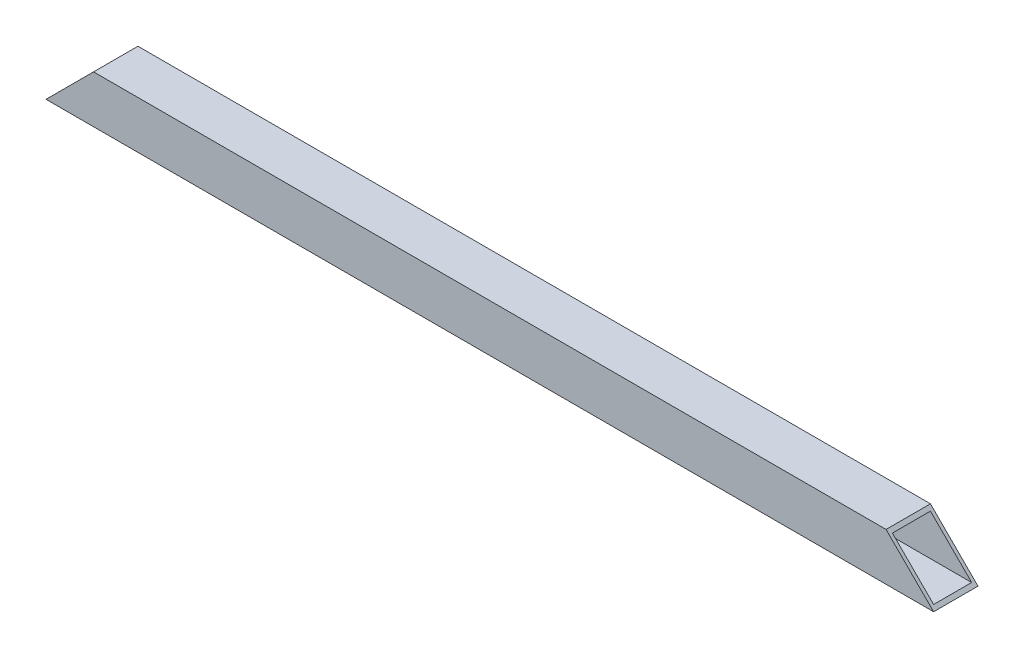
SolidWorks part; units mm, degrees
ref_plane "Спереди" through (0, 0, 0) normal (0, 0, 1) x (1, 0, 0)
ref_plane "Сверху" through (0, 0, 0) normal (0, 1, 0) x (1, 0, 0)
ref_plane "Справа" through (0, 0, 0) normal (1, 0, 0) x (0, 0, -1)
sketch "Эскиз2" plane through (0, 0, 0) normal (1, 0, 0) x (0, 0, -1)
  line L1 (-35, 37.5) -> (35, 37.5)
  line L2 (-35, 37.5) -> (-35, -37.5)
  line L3 (-35, -37.5) -> (35, -37.5)
  line L4 (35, 37.5) -> (35, -37.5)
  line L5 (-35, 37.5) -> (35, -37.5) construction
  line L6 (-35, -37.5) -> (35, 37.5) construction
  point P0 (0, 0)
extrude "Вытянуть-Тонкостенный1" add sketch "Эскиз2" along normal blind 1400 thin
sketch "Эскиз3" plane through (0, 0, -35) normal (0, 0, -1) x (-1, 0, 0)
  line L0 (-1400, -37.5) -> (-1325, 37.5)
  line L1 (-1400, 37.5) -> (0, 37.5) construction
  line L2 (-1325, 37.5) -> (-75, 37.5)
  line L3 (-75, 37.5) -> (0, -37.5)
  line L4 (0, -37.5) -> (-1400, -37.5)
extrude "Вырез-Вытянуть1" cut sketch "Эскиз3" against normal through all flip side to cut
